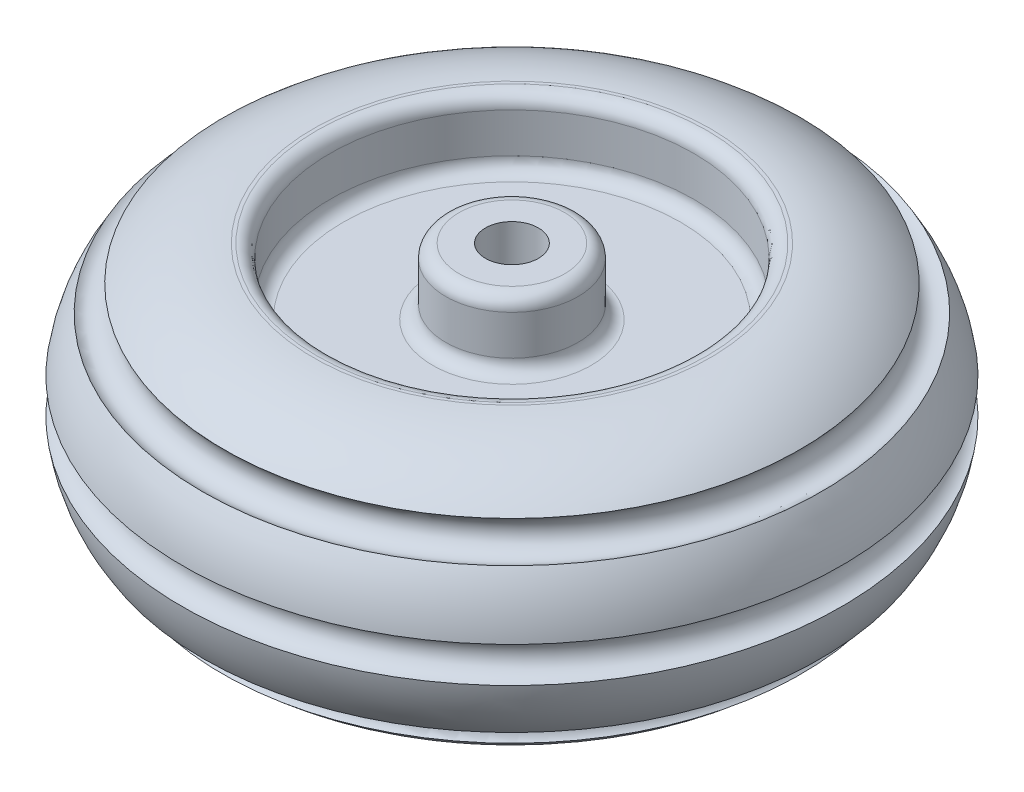
SolidWorks part; units mm, degrees
ref_plane "Front Plane" through (0, 0, 0) normal (0, 0, 1) x (1, 0, 0)
ref_plane "Top Plane" through (0, 0, 0) normal (0, 1, 0) x (1, 0, 0)
ref_plane "Right Plane" through (0, 0, 0) normal (1, 0, 0) x (0, 0, -1)
sketch "Sketch2" plane through (0, 0, 0) normal (0, 0, 1) x (1, 0, 0)
  line L0 (0, 0) -> (1138.751, 0) construction
  line L1 (0, 0) -> (0, 1292.1231) construction
  line L2 (22.5, -100) -> (22.5, 100)
  line L3 (22.5, 100) -> (62.5, 100)
  line L4 (72.5, 90) -> (72.5, 60)
  line L5 (82.5, 50) -> (150, 50)
  line L6 (160, 60) -> (160, 90)
  line L7 (170, 100) -> (172.5, 100)
  line L8 (170, -100) -> (172.5, -100)
  line L9 (160, -60) -> (160, -90)
  line L10 (82.5, -50) -> (150, -50)
  line L11 (72.5, -90) -> (72.5, -60)
  line L12 (22.5, -100) -> (62.5, -100)
  arc A0 (172.5, 100) -> (240.137, 73.6562) centre (172.5, 0) cw
  arc A1 (170, -100) -> (160, -90) centre (170, -90) cw
  arc A2 (72.5, -90) -> (62.5, -100) centre (62.5, -90) cw
  arc A3 (82.5, -50) -> (72.5, -60) centre (82.5, -60) ccw
  arc A4 (160, -60) -> (150, -50) centre (150, -60) ccw
  arc A5 (160, 90) -> (170, 100) centre (170, 90) cw
  arc A6 (150, 50) -> (160, 60) centre (150, 60) ccw
  arc A7 (72.5, 60) -> (82.5, 50) centre (82.5, 60) ccw
  arc A8 (62.5, 100) -> (72.5, 90) centre (62.5, 90) cw
  arc A9 (240.137, 73.6562) -> (256.4658, 54.3115) centre (248.916, 64.5026) ccw
  arc A10 (271.5921, 13.4448) -> (271.5921, -13.4448) centre (272.5, 0) ccw
  arc A11 (255.7525, -55.3987) -> (241.089, -72.7705) centre (248.916, -64.5026) ccw
  arc A12 (256.4658, 54.3115) -> (271.5921, 13.4448) centre (172.5, 0) cw
  arc A13 (271.5921, -13.4448) -> (255.7525, -55.3987) centre (172.5, 0) cw
  arc A14 (241.089, -72.7705) -> (172.5, -100) centre (172.5, 0) cw
  point P14 (22.5, 0)
  point P20 (160, -100)
  point P23 (72.5, -100)
  point P26 (72.5, -50)
  point P29 (160, -50)
  point P32 (160, 100)
  point P35 (160, 50)
  point P38 (72.5, 50)
  point P41 (72.5, 100)
  dimension "D6" = 100
  dimension "D9" = 12.5
  dimension "D10" = 10
  dimension "D8" = 10
  dimension "D11" = 10
  dimension "D1" = 20
  dimension "D2" = 100
  dimension "D3" = 50
  dimension "D4" = 87.5
  dimension "D5" = 12.5
  dimension "D7" = 50
revolve "Revolve2" add sketch "Sketch2" angle 360 about L2
sketch "Sketch3" plane through (0, -100, 0) normal (0, -1, 0) x (1, 0, 0)
  circle A0 centre (22.5, 0) radius 20
  dimension "D1" = 40
extrude "Cut-Extrude1" cut sketch "Sketch3" against normal through all
